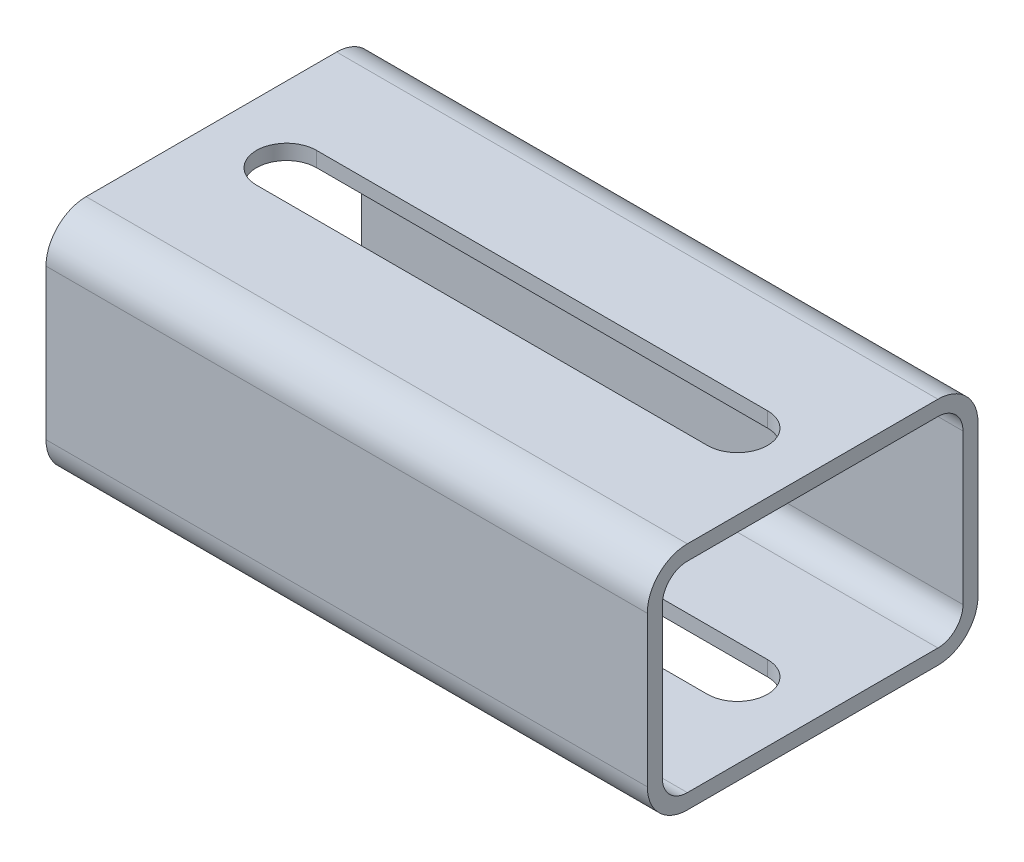
SolidWorks part; units mm, degrees
ref_plane "Front Plane" through (0, 0, 0) normal (0, 0, 1) x (1, 0, 0)
ref_plane "Top Plane" through (0, 0, 0) normal (0, 1, 0) x (1, 0, 0)
ref_plane "Right Plane" through (0, 0, 0) normal (1, 0, 0) x (0, 0, -1)
sketch "Sketch1" plane through (0, 0, 0) normal (1, 0, 0) x (0, 0, -1)
  line L1 (-25, 20) -> (25, 20)
  line L2 (-30, 15) -> (-30, -15)
  line L3 (-25, -20) -> (25, -20)
  line L4 (30, 15) -> (30, -15)
  line L5 (-30, 20) -> (30, -20) construction
  line L6 (-30, -20) -> (30, 20) construction
  arc A0 (-30, -15) -> (-25, -20) centre (-25, -15) ccw
  arc A1 (25, -20) -> (30, -15) centre (25, -15) ccw
  arc A2 (25, 20) -> (30, 15) centre (25, 15) cw
  arc A3 (-25, 20) -> (-30, 15) centre (-25, 15) ccw
  point P0 (0, 0)
  dimension "D3" = 5
  dimension "Width" = 60
  dimension "Height" = 40
extrude "Extrude-Thin1" add sketch "Sketch1" along normal mid plane 120 thin thin type one direction wall 3
sketch "Sketch2" plane through (0, 23, 0) normal (0, 1, 0) x (1, 0, 0)
  line L0 (-45, 0) -> (45, 0) construction
  line L1 (-45, 6) -> (45, 6)
  line L2 (-45, -6) -> (45, -6)
  arc A0 (-45, 6) -> (-45, -6) centre (-45, 0) ccw
  arc A1 (45, -6) -> (45, 6) centre (45, 0) ccw
  point P3 (0, 0)
  dimension "D2" = 6
  dimension "D1" = 90
extrude "Cut-Extrude1" cut sketch "Sketch2" against normal through all
